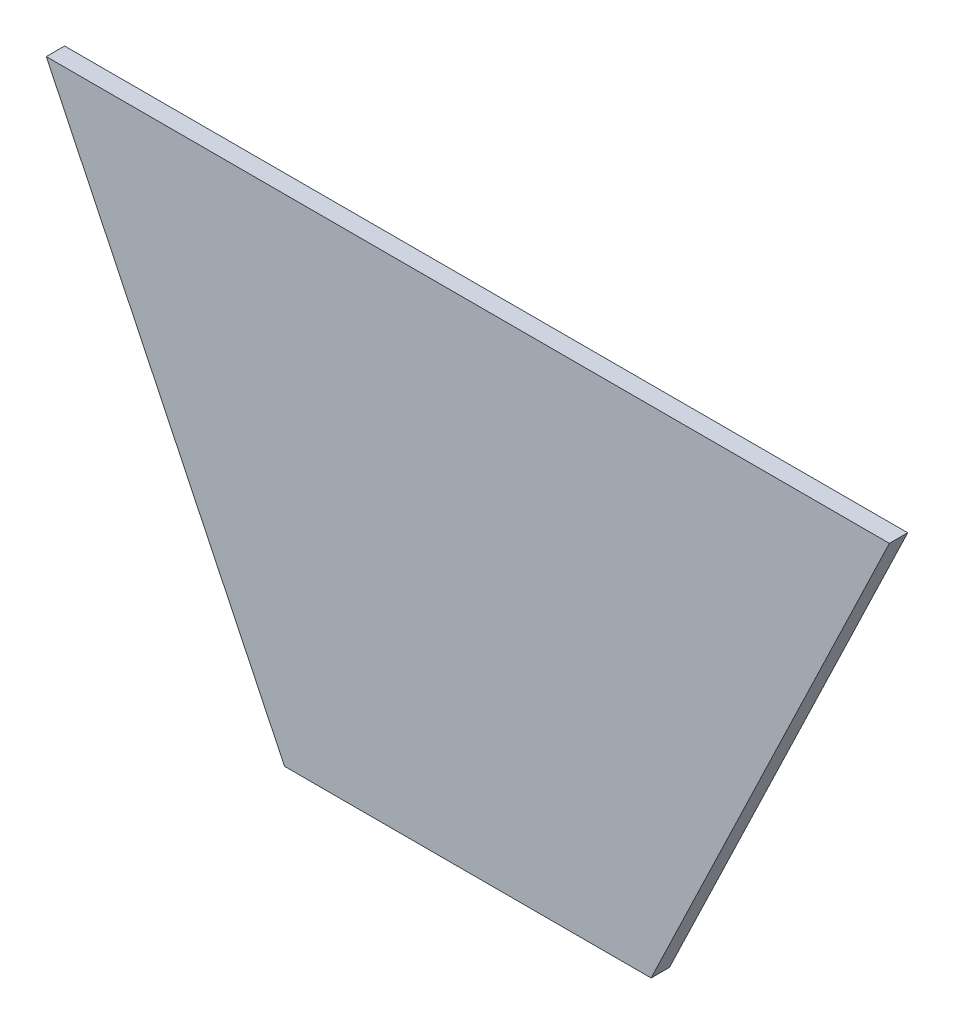
SolidWorks part; units mm, degrees
ref_plane "Front Plane" through (0, 0, 0) normal (0, 0, 1) x (1, 0, 0)
ref_plane "Top Plane" through (0, 0, 0) normal (0, 1, 0) x (1, 0, 0)
ref_plane "Right Plane" through (0, 0, 0) normal (1, 0, 0) x (0, 0, -1)
sketch "Sketch1" plane through (0, 0, 0) normal (0, 0, 1) x (1, 0, 0)
  line L0 (-100, 0) -> (100, 0)
  line L1 (100, 0) -> (230, 270.3701)
  line L2 (230, 270.3701) -> (-230, 270.3701)
  line L3 (-230, 270.3701) -> (-100, 0)
  point P3 (0, 0)
  point P7 (-166.0306, 139.0761)
  dimension "D1" = 200
  dimension "D2" = 300
  dimension "D3" = 460
  dimension "D4" = 300
extrude "Boss-Extrude1" add sketch "Sketch1" along normal blind 10
